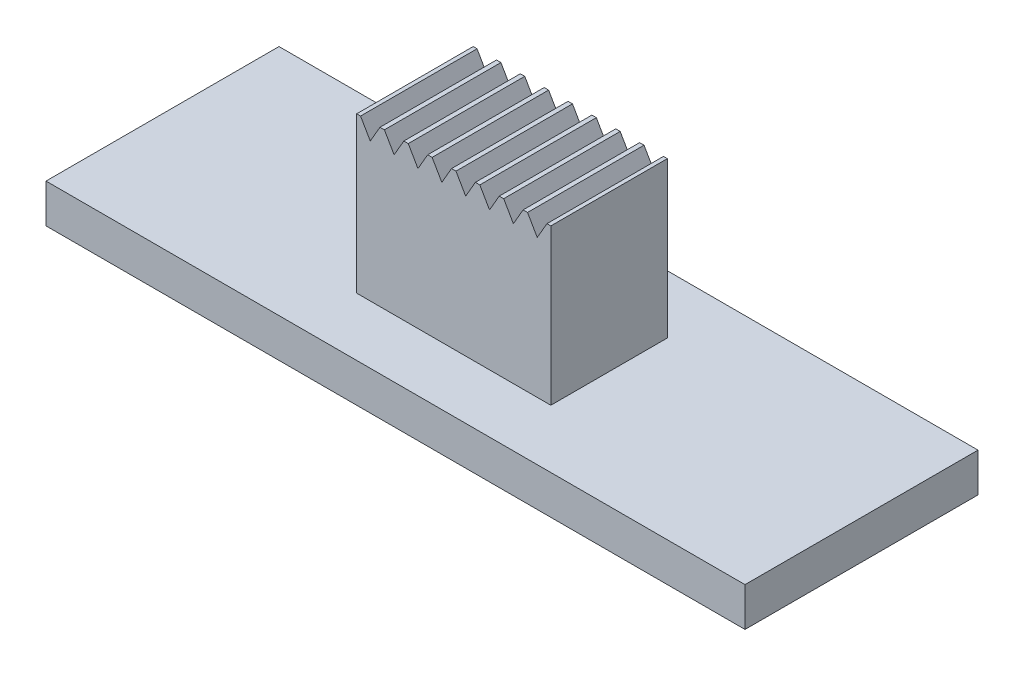
SolidWorks part; units mm, degrees
material "PBT General Purpose"
ref_plane "Front Plane" through (0, 0, 0) normal (0, 0, 1) x (1, 0, 0)
ref_plane "Top Plane" through (0, 0, 0) normal (0, 1, 0) x (1, 0, 0)
ref_plane "Right Plane" through (0, 0, 0) normal (1, 0, 0) x (0, 0, -1)
sketch "Sketch1" plane through (0, 0, 0) normal (0, 1, 0) x (1, 0, 0)
  line L1 (-9, -3) -> (9, -3)
  line L2 (-9, -3) -> (-9, 3)
  line L3 (-9, 3) -> (9, 3)
  line L4 (9, -3) -> (9, 3)
  line L5 (-9, -3) -> (9, 3) construction
  line L6 (-9, 3) -> (9, -3) construction
  point P0 (0, 0)
  dimension "D1" = 6
  dimension "D2" = 18
extrude "Boss-Extrude1" add sketch "Sketch1" along normal blind 1
sketch "Sketch2" plane through (0, 1, 0) normal (0, 1, 0) x (1, 0, 0)
  line L1 (-2.5, 1.5) -> (2.5, 1.5)
  line L2 (-2.5, 1.5) -> (-2.5, -1.5)
  line L3 (-2.5, -1.5) -> (2.5, -1.5)
  line L4 (2.5, 1.5) -> (2.5, -1.5)
  line L5 (-2.5, 1.5) -> (2.5, -1.5) construction
  line L6 (-2.5, -1.5) -> (2.5, 1.5) construction
  point P0 (0, 0)
  dimension "D1" = 3
  dimension "D2" = 5
extrude "Boss-Extrude2" add sketch "Sketch2" along normal blind 4
sketch "Sketch3" plane through (0, 0, 1.5) normal (0, 0, 1) x (1, 0, 0)
  line L0 (-2.5, 5) -> (-2.5, 1) construction
  line L1 (-2.15, 4.567) -> (-1.9, 5)
  line L2 (-1.9, 5) -> (-2.4, 5)
  line L3 (-2.4, 5) -> (-2.15, 4.567)
  line L5 (-2.5, 5) -> (2.5, 5) construction
  dimension "D1" = 0.5
  dimension "D2" = 0.35
extrude "Cut-Extrude1" cut sketch "Sketch3" against normal through all both and the other way through all
sketch "Sketch4" plane through (0, 0, 1.5) normal (0, 0, 1) x (1, 0, 0)
  line L0 (2.5, 5) -> (2.5, 1) construction
  line L1 (-1.9, 5) -> (2.5, 5) construction
  point P0 (2.15, 5)
  dimension "D1" = 0.35
pattern_linear "LPattern1" count 8 spacing 0.6143 along (1, 0, 0) of "Cut-Extrude1"
